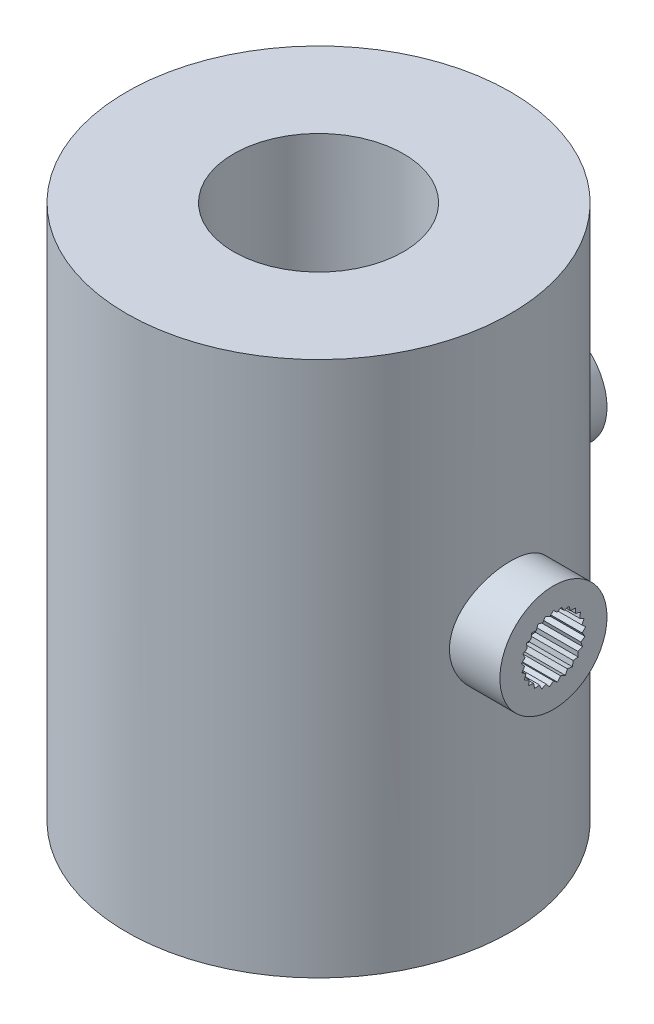
SolidWorks part; units mm, degrees
ref_plane "Front Plane" through (0, 0, 0) normal (0, 0, 1) x (1, 0, 0)
ref_plane "Top Plane" through (0, 0, 0) normal (0, 1, 0) x (1, 0, 0)
ref_plane "Right Plane" through (0, 0, 0) normal (1, 0, 0) x (0, 0, -1)
sketch "Sketch1" plane through (0, 0, 0) normal (0, 1, 0) x (1, 0, 0)
  circle A0 centre (0, 0) radius 17.9289
  dimension "D1" = 35.8579
extrude "Boss-Extrude1" add sketch "Sketch1" along normal blind 10 contours A0
sketch "Sketch2" plane through (0, 10, 0) normal (0, 1, 0) x (1, 0, 0)
  circle A2 centre (0, 0) radius 7.9289
  circle A3 centre (0, 0) radius 7.9289
  dimension "D1" = 10
extrude "Cut-Extrude1" cut sketch "Sketch2" against normal through all
sketch "Sketch3" plane through (0, 0, 0) normal (0, 0, 1) x (1, 0, 0)
  line L0 (0, 0) -> (0, 10) construction
  line L1 (-17.9289, 0) -> (17.9289, 0) construction
  line L2 (7.9289, 10) -> (-7.9289, 10) construction
  line L3 (0, 5) -> (17.9289, 5) construction
  line L4 (17.9289, 0) -> (17.9289, 10) construction
  line L5 (0, 5) -> (-17.9289, 5) construction
  line L6 (-17.9289, 10) -> (-17.9289, 0) construction
  line L7 (17.9289, 5) -> (21.9289, 5) construction
  dimension "D1" = 4
ref_plane "Plane1" through (21.9289, 0, 0) normal (1, 0, 0) x (0, 0, -1)
sketch "Sketch4" plane through (21.9289, 0, 0) normal (1, 0, 0) x (0, 0, -1)
  line L0 (0, 0) -> (0, 10) construction
  line L1 (17.9289, 10) -> (-17.9289, 10) construction
  circle A0 centre (0, 5) radius 5
extrude "Boss-Extrude2" add sketch "Sketch4" against normal up to surface (4.7113 mm away)
sketch "Sketch10" plane through (0, 0, 0) normal (1, 0, 0) x (0, 0, -1)
  line L0 (0, 0) -> (0, 10) construction
  line L1 (0, 5) -> (-17.9289, 5) construction
  line L2 (-17.9289, 10) -> (-17.9289, 0) construction
  line L3 (0, 5) -> (17.9289, 5) construction
  line L4 (17.9289, 5) -> (21.9289, 5) construction
  circle A0 centre (0, 5) radius 5 construction
  dimension "D1" = 4
ref_plane "Plane4" through (0, 0, -21.9289) normal (0, 0, 1) x (1, 0, 0)
sketch "Sketch11" plane through (0, 0, -21.9289) normal (0, 0, 1) x (1, 0, 0)
  line L0 (17.9289, 10) -> (-17.9289, 10) construction
  circle A0 centre (0, 5) radius 5
extrude "Boss-Extrude5" add sketch "Sketch11" along normal up to surface (4.7113 mm away)
sketch "Sketch14" plane through (0, 0, -21.9289) normal (0, 0, -1) x (-1, 0, 0)
  line L0 (0, 5) -> (0, 8) construction
  line L1 (0, 5) -> (0.376, 7.9763) construction
  line L2 (0, 5) -> (-0.376, 7.9763) construction
  line L3 (0, 8) -> (-0.3384, 7.6786)
  line L4 (0, 8) -> (0.3384, 7.6786)
  line L5 (0.7461, 7.9057) -> (0.3384, 7.6786)
  line L6 (0.7461, 7.9057) -> (0.9939, 7.5102)
  line L7 (1.4453, 7.6289) -> (0.9939, 7.5102)
  line L8 (1.4453, 7.6289) -> (1.5869, 7.1842)
  line L9 (2.0536, 7.1869) -> (1.5869, 7.1842)
  line L10 (2.0536, 7.1869) -> (2.0803, 6.7209)
  line L11 (2.533, 6.6075) -> (2.0803, 6.7209)
  line L12 (2.533, 6.6075) -> (2.4429, 6.1495)
  line L13 (2.8532, 5.9271) -> (2.4429, 6.1495)
  line L14 (2.8532, 5.9271) -> (2.652, 5.5059)
  line L15 (2.9941, 5.1884) -> (2.652, 5.5059)
  line L16 (2.9941, 5.1884) -> (2.6945, 4.8305)
  line L17 (2.9469, 4.4379) -> (2.6945, 4.8305)
  line L18 (2.9469, 4.4379) -> (2.5677, 4.1657)
  line L19 (2.7145, 3.7227) -> (2.5677, 4.1657)
  line L20 (2.7145, 3.7227) -> (2.2796, 3.5534)
  line L21 (2.3115, 3.0877) -> (2.2796, 3.5534)
  line L22 (2.3115, 3.0877) -> (1.8482, 3.0319)
  line L23 (1.7634, 2.5729) -> (1.8482, 3.0319)
  line L24 (1.7634, 2.5729) -> (1.3007, 2.6341)
  line L25 (1.1044, 2.2107) -> (1.3007, 2.6341)
  line L26 (1.1044, 2.2107) -> (0.6714, 2.385)
  line L27 (0.376, 2.0237) -> (0.6714, 2.385)
  line L28 (0.376, 2.0237) -> (0, 2.3002)
  line L29 (-0.376, 2.0237) -> (0, 2.3002)
  line L30 (-0.376, 2.0237) -> (-0.6714, 2.385)
  line L31 (-1.1044, 2.2107) -> (-0.6714, 2.385)
  line L32 (-1.1044, 2.2107) -> (-1.3007, 2.6341)
  line L33 (-1.7634, 2.5729) -> (-1.3007, 2.6341)
  line L34 (-1.7634, 2.5729) -> (-1.8482, 3.0319)
  line L35 (-2.3115, 3.0877) -> (-1.8482, 3.0319)
  line L36 (-2.3115, 3.0877) -> (-2.2796, 3.5534)
  line L37 (-2.7145, 3.7227) -> (-2.2796, 3.5534)
  line L38 (-2.7145, 3.7227) -> (-2.5677, 4.1657)
  line L39 (-2.9469, 4.4379) -> (-2.5677, 4.1657)
  line L40 (-2.9469, 4.4379) -> (-2.6945, 4.8305)
  line L41 (-2.9941, 5.1884) -> (-2.6945, 4.8305)
  line L42 (-2.9941, 5.1884) -> (-2.652, 5.5059)
  line L43 (-2.8532, 5.9271) -> (-2.652, 5.5059)
  line L44 (-2.8532, 5.9271) -> (-2.4429, 6.1495)
  line L45 (-2.533, 6.6075) -> (-2.4429, 6.1495)
  line L46 (-2.533, 6.6075) -> (-2.0803, 6.7209)
  line L47 (-2.0536, 7.1869) -> (-2.0803, 6.7209)
  line L48 (-2.0536, 7.1869) -> (-1.5869, 7.1842)
  line L49 (-1.4453, 7.6289) -> (-1.5869, 7.1842)
  line L50 (-1.4453, 7.6289) -> (-0.9939, 7.5102)
  line L51 (-0.7461, 7.9057) -> (-0.9939, 7.5102)
  line L52 (-0.7461, 7.9057) -> (-0.3384, 7.6786)
  circle A0 centre (0, 5) radius 3 construction
  point P19 (0, 5)
  point P83 (0, 5)
  dimension "D1" = 6
  dimension "D2" = 14.4
  dimension "D3" = 7.2
  dimension "D4" = 53.67
  dimension "D5" = 53.67
  dimension "D6" = 25
extrude "Cut-Extrude5" cut sketch "Sketch14" against normal blind 4
pattern_circular "CirPattern1" count 2 over 270 about axis through (0, 0, 0) along (0, 1, 0) of "Cut-Extrude5"
sketch "Sketch21" plane through (0, 10, 0) normal (0, 1, 0) x (1, 0, 0)
  circle A0 centre (0, 0) radius 7.9289 construction
  circle A1 centre (0, 0) radius 7.9289
  arc A2 (17.9289, 0) -> (0, 17.9289) centre (0, 0) ccw
  arc A3 (0, 17.9289) -> (17.9289, 0) centre (0, 0) ccw
  arc A4 (17.9289, 0) -> (0, 17.9289) centre (0, 0) ccw
  arc A5 (0, 17.9289) -> (17.9289, 0) centre (0, 0) ccw
  dimension "D1" = 0
extrude "Boss-Extrude6" add sketch "Sketch21" along normal blind 20
sketch "Sketch22" plane through (0, 0, 0) normal (0, -1, 0) x (1, 0, 0)
  circle A0 centre (0, 0) radius 7.9289 construction
  circle A1 centre (0, 0) radius 7.9289
  arc A2 (0, -17.9289) -> (17.9289, 0) centre (0, 0) ccw
  arc A3 (17.9289, 0) -> (0, -17.9289) centre (0, 0) ccw
  arc A4 (0, -17.9289) -> (17.9289, 0) centre (0, 0) ccw
  arc A5 (17.9289, 0) -> (0, -17.9289) centre (0, 0) ccw
  dimension "D1" = 0
extrude "Boss-Extrude7" add sketch "Sketch22" along normal blind 20
